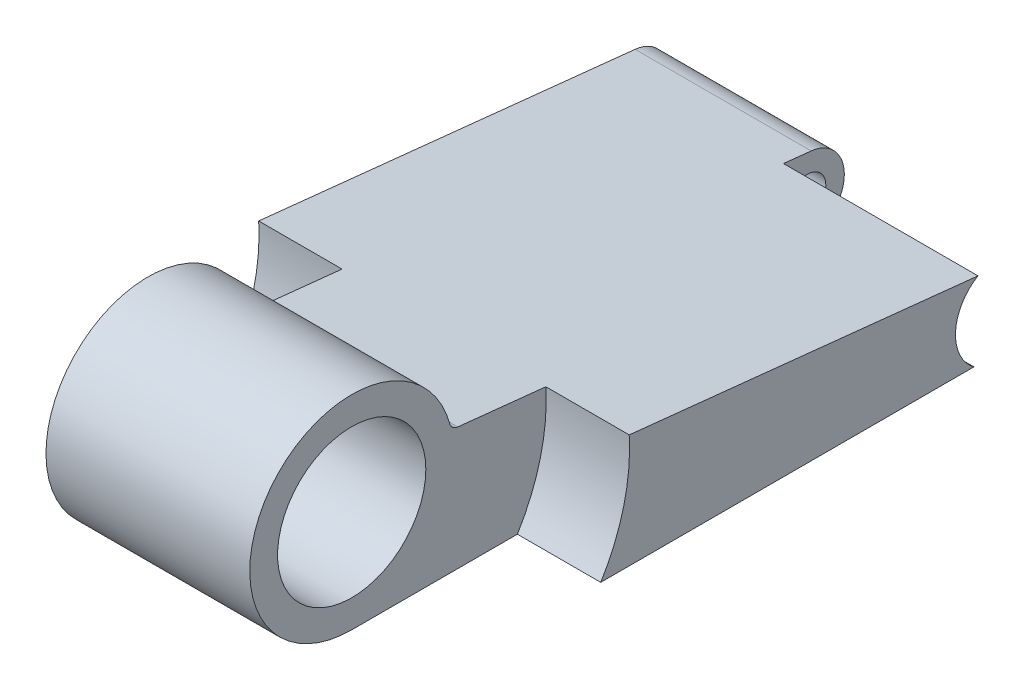
SolidWorks part; units mm, degrees
material "AISI 1035 Steel (SS)"
ref_plane "Front Plane" through (0, 0, 0) normal (0, 0, 1) x (1, 0, 0)
ref_plane "Top Plane" through (0, 0, 0) normal (0, 1, 0) x (1, 0, 0)
ref_plane "Right Plane" through (0, 0, 0) normal (1, 0, 0) x (0, 0, -1)
sketch "Sketch1" plane through (0, 0, 0) normal (1, 0, 0) x (0, 0, -1)
  line L0 (-6.1021, -4.3129) -> (17.8829, -4.3129)
  line L4 (18.0467, -1.1846) -> (-1.8863, 0.9101)
  arc A0 (-1.8863, 0.9101) -> (-6.1021, -4.3129) centre (-6.1021, 0) ccw
  arc A1 (17.8829, -4.3129) -> (18.0467, -1.1846) centre (17.8829, -2.7445) ccw
  circle A2 centre (-6.1021, 0) radius 3.1369
  circle A3 centre (17.8829, -2.7445) radius 0.7849
  point P6 (47.7864, -4.3117)
  point P9 (7.2177, -4.3117)
  point P10 (7.5171, -0.0792)
extrude "Boss-Extrude1" add sketch "Sketch1" against normal blind 15.682
fillet "Fillet1" radius 0.3912 1 edges at (-7.841, 0.9101, 1.8863)
sketch "Sketch2" plane through (0, 0, 0) normal (1, 0, 0) x (0, 0, -1)
  circle A0 centre (-6.1021, 0) radius 8.2321
extrude "Cut-Extrude1" cut sketch "Sketch2" against normal blind 3.5281
sketch "Sketch3" plane through (-15.682, 0, 0) normal (-1, 0, 0) x (0, 0, 1)
  circle A0 centre (6.1021, 0) radius 8.2321
extrude "Cut-Extrude2" cut sketch "Sketch3" against normal blind 3.5281
sketch "Sketch4" plane through (0, 0, 0) normal (1, 0, 0) x (0, 0, -1)
  circle A0 centre (17.8829, -2.7445) radius 1.9609
extrude "Cut-Extrude3" cut sketch "Sketch4" against normal blind 8.2321
